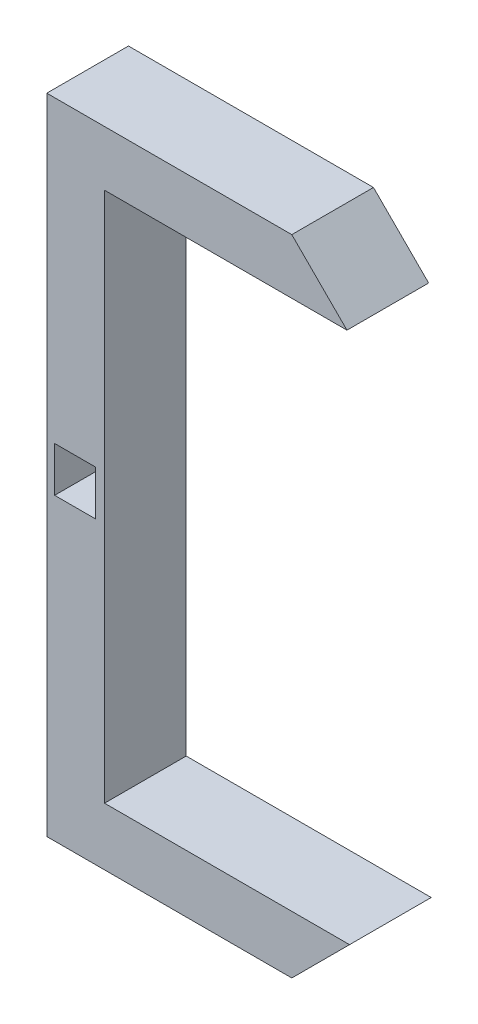
SolidWorks part; units mm, degrees
ref_plane "Front Plane" through (0, 0, 0) normal (0, 0, 1) x (1, 0, 0)
ref_plane "Top Plane" through (0, 0, 0) normal (0, 1, 0) x (1, 0, 0)
ref_plane "Right Plane" through (0, 0, 0) normal (1, 0, 0) x (0, 0, -1)
sketch "Sketch1" plane through (0, 0, 0) normal (0, 0, 1) x (1, 0, 0)
  line L0 (-15.0052, 49.7146) -> (-44.6896, 49.7146)
  line L1 (-15.0052, 49.7146) -> (-21.7607, 56.4701)
  line L3 (-51.7607, 56.4701) -> (-51.7607, -18.2144)
  line L4 (-44.6896, 49.7146) -> (-44.6896, -15.2854)
  line L5 (-44.6896, -15.2854) -> (-14.6896, -15.2854)
  line L6 (-14.6896, -15.2854) -> (-21.7607, -22.3565)
  line L7 (-21.7607, -22.3565) -> (-51.7607, -22.3565)
  line L8 (-51.7607, -22.3565) -> (-51.7607, -18.2144)
  line L9 (-51.7607, 56.4701) -> (-21.7607, 56.4701)
extrude "Boss-Extrude1" add sketch "Sketch1" along normal blind 10
sketch "Sketch2" plane through (0, 0, 0) normal (0, 0, 1) x (1, 0, 0)
  line L8 (-50.7987, 19.8068) -> (-45.7987, 19.8068)
  line L9 (-50.7987, 19.8068) -> (-50.7987, 14.3068)
  line L10 (-50.7987, 14.3068) -> (-45.7987, 14.3068)
  line L11 (-45.7987, 19.8068) -> (-45.7987, 14.3068)
  line L12 (-50.7987, 19.8068) -> (-45.7987, 14.3068) construction
  line L13 (-50.7987, 14.3068) -> (-45.7987, 19.8068) construction
extrude "Cut-Extrude2" cut sketch "Sketch2" against normal blind 10 and the other way through all
